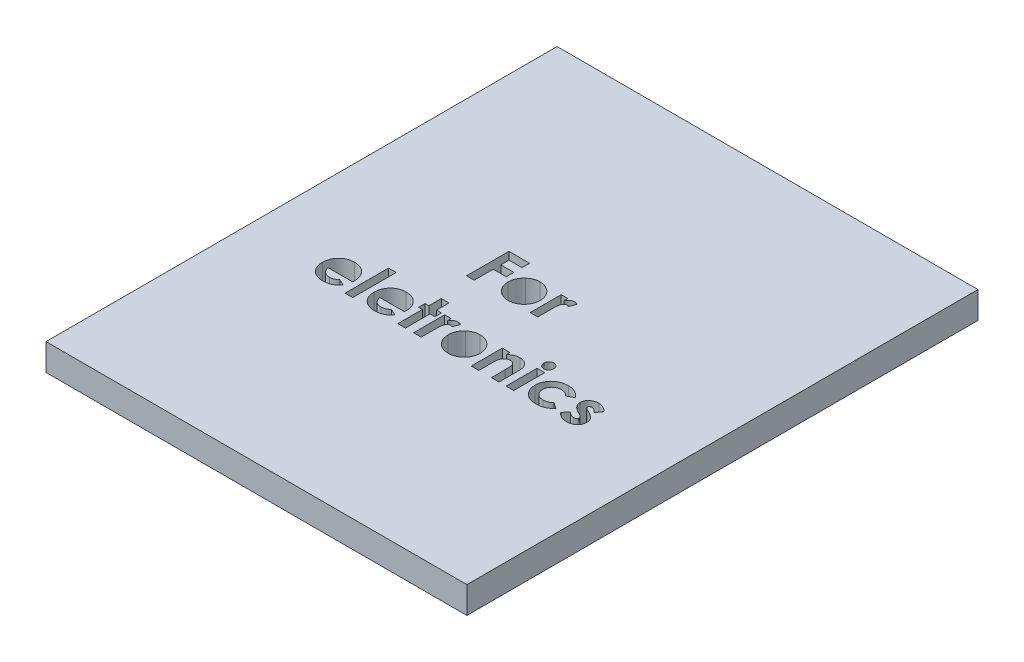
SolidWorks part; units mm, degrees
ref_plane "Front" through (0, 0, 0) normal (0, 0, 1) x (1, 0, 0)
ref_plane "Top" through (0, 0, 0) normal (0, 1, 0) x (1, 0, 0)
ref_plane "Right" through (0, 0, 0) normal (1, 0, 0) x (0, 0, -1)
sketch "Sketch1" plane through (0, 0, 0) normal (0, 1, 0) x (1, 0, 0)
  line L1 (-63, 81.5) -> (0, 81.5)
  line L2 (-63, 81.5) -> (-63, 0)
  line L3 (-63, 0) -> (0, 0)
  line L4 (0, 81.5) -> (0, 0)
  dimension "D1" = 81.5
  dimension "D2" = 63
extrude "Boss-Extrude1" add sketch "Sketch1" along normal blind 4
sketch "Sketch2" plane through (0, 4, 0) normal (0, 1, 0) x (1, 0, 0)
  text T0 "<b>     For</b>\r\n<b>eletronics</b>"
  dimension "D1" = 40
  dimension "D2" = 53
extrude "Cut-Extrude1" cut sketch "Sketch2" against normal through all
sketch "Sketch3" plane through (0, 4, 0) normal (0, 1, 0) x (1, 0, 0)
  line L0 (0, 0) -> (0, 81.5) construction
  line L1 (-63, 76.5) -> (0, 76.5)
  line L2 (-63, 76.5) -> (-63, 81.5)
  line L3 (-63, 81.5) -> (0, 81.5)
  line L4 (0, 76.5) -> (0, 81.5)
  dimension "D1" = 5
extrude "Cut-Extrude2" cut sketch "Sketch3" against normal through all
